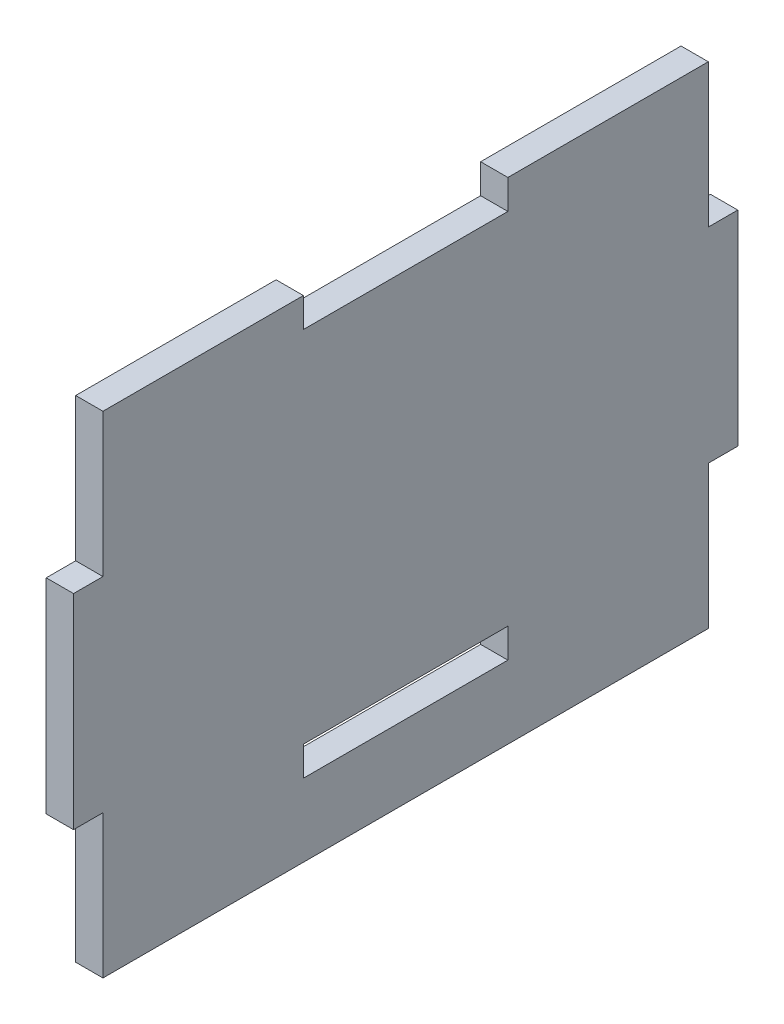
SolidWorks part; units mm, degrees
ref_plane "Front Plane" through (0, 0, 0) normal (0, 0, 1) x (1, 0, 0)
ref_plane "Top Plane" through (0, 0, 0) normal (0, 1, 0) x (1, 0, 0)
ref_plane "Right Plane" through (0, 0, 0) normal (1, 0, 0) x (0, 0, -1)
sketch "Sketch1" plane through (0, 0, 0) normal (1, 0, 0) x (0, 0, -1)
  line L1 (28.194, -22.86) -> (-28.194, -22.86)
  line L2 (28.194, -22.86) -> (28.194, 22.86)
  line L3 (28.194, 22.86) -> (-28.194, 22.86)
  line L4 (-28.194, -22.86) -> (-28.194, 22.86)
  line L5 (28.194, -22.86) -> (-28.194, 22.86) construction
  line L6 (28.194, 22.86) -> (-28.194, -22.86) construction
  point P0 (0, 0)
  dimension "D1" = 56.388
  dimension "D2" = 45.72
extrude "Boss-Extrude1" add sketch "Sketch1" along normal blind 2.54
sketch "Sketch2" plane through (2.54, 0, 0) normal (1, 0, 0) x (0, 0, -1)
  line L0 (-28.194, 22.86) -> (-28.194, -22.86) construction
  line L1 (-30.9372, 9.525) -> (-28.194, 9.525)
  line L2 (-30.9372, 9.525) -> (-30.9372, -9.525)
  line L3 (-30.9372, -9.525) -> (-28.194, -9.525)
  line L4 (-28.194, 9.525) -> (-28.194, -9.525)
  line L5 (-30.9372, 9.525) -> (-28.194, -9.525) construction
  line L6 (-30.9372, -9.525) -> (-28.194, 9.525) construction
  line L7 (28.194, -22.86) -> (28.194, 22.86) construction
  line L8 (30.9372, 9.525) -> (28.194, 9.525)
  line L9 (30.9372, 9.525) -> (30.9372, -9.525)
  line L10 (30.9372, -9.525) -> (28.194, -9.525)
  line L11 (28.194, 9.525) -> (28.194, -9.525)
  line L12 (30.9372, 9.525) -> (28.194, -9.525) construction
  line L13 (30.9372, -9.525) -> (28.194, 9.525) construction
  line L14 (-29.5656, 0) -> (29.5656, 0) construction
  point P0 (-29.5656, 0)
  point P7 (29.5656, 0)
  dimension "D1" = 19.05
  dimension "D2" = 2.7432
extrude "Boss-Extrude2" add sketch "Sketch2" against normal up to surface (2.54 mm away) up to face at (0, 0, 0)
sketch "Sketch3" plane through (2.54, 0, 0) normal (1, 0, 0) x (0, 0, -1)
  line L0 (28.194, 22.86) -> (-28.194, 22.86) construction
  line L1 (-9.525, 20.1168) -> (9.525, 20.1168)
  line L2 (-9.525, 20.1168) -> (-9.525, 22.86)
  line L3 (-9.525, 22.86) -> (9.525, 22.86)
  line L4 (9.525, 20.1168) -> (9.525, 22.86)
  line L5 (-9.525, 20.1168) -> (9.525, 22.86) construction
  line L6 (-9.525, 22.86) -> (9.525, 20.1168) construction
  line L7 (-28.194, -22.86) -> (28.194, -22.86) construction
  line L8 (9.525, -13.335) -> (-9.525, -13.335)
  line L9 (9.525, -13.335) -> (9.525, -16.0782)
  line L10 (9.525, -16.0782) -> (-9.525, -16.0782)
  line L11 (-9.525, -13.335) -> (-9.525, -16.0782)
  line L12 (9.525, -13.335) -> (-9.525, -16.0782) construction
  line L13 (9.525, -16.0782) -> (-9.525, -13.335) construction
  line L14 (0, -14.7066) -> (0, 21.4884) construction
  point P0 (0, 21.4884)
  point P7 (0, -14.7066)
  point P16 (0, 0)
  dimension "D1" = 19.05
  dimension "D2" = 9.525
  dimension "D3" = 2.7432
extrude "Cut-Extrude1" cut sketch "Sketch3" against normal through all
